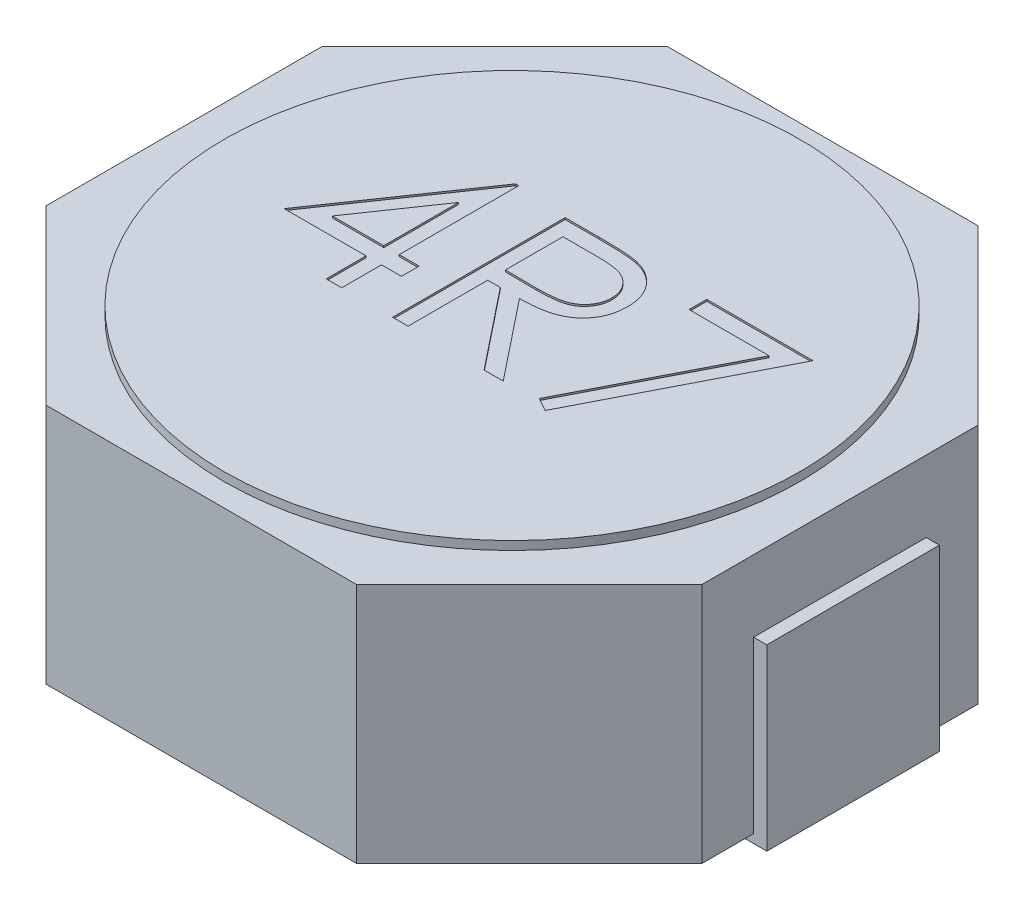
SolidWorks part; units mm, degrees
ref_plane "Front Plane" through (0, 0, 0) normal (0, 0, 1) x (1, 0, 0)
ref_plane "Top Plane" through (0, 0, 0) normal (0, 1, 0) x (1, 0, 0)
ref_plane "Right Plane" through (0, 0, 0) normal (1, 0, 0) x (0, 0, -1)
sketch "Sketch1" plane through (0, 0, 0) normal (0, 1, 0) x (1, 0, 0)
  line L0 (-0.9, 1.8) -> (-1.9, 0.8)
  line L1 (-0.9, 1.8) -> (0.9, 1.8)
  line L2 (-1.9, 0.8) -> (-1.9, -0.8)
  line L3 (-0.9, -1.8) -> (0.9, -1.8)
  line L4 (1.9, 0.8) -> (1.9, -0.8)
  line L5 (-1.9, 1.8) -> (1.9, -1.8) construction
  line L6 (-1.9, -1.8) -> (1.9, 1.8) construction
  line L7 (0.9, -1.8) -> (1.9, -0.8)
  line L8 (0.9, 1.8) -> (1.9, 0.8)
  line L9 (-1.9, -0.8) -> (-0.9, -1.8)
  point P0 (0, 0)
  dimension "D1" = 3.8
  dimension "D2" = 3.6
extrude "Boss-Extrude1" add sketch "Sketch1" along normal blind 1.4
sketch "Sketch2" plane through (0, 1.4, 0) normal (0, 1, 0) x (1, 0, 0)
  circle A0 centre (0, 0) radius 1.6679
extrude "Boss-Extrude2" add sketch "Sketch2" along normal blind 0.05
sketch "Sketch3" plane through (0, 0, 0) normal (0, 0, 1) x (1, 0, 0)
  line L0 (-1.9764, 0.9857) -> (-1.9764, -0.0499)
  line L1 (-1.9764, -0.0499) -> (-1.2507, -0.0499)
extrude "Extrude-Thin1" add sketch "Sketch3" along normal mid plane 1 thin thin type one direction reverse wall 0.1
mirror "Mirror1" about plane through (0, 0, 0) normal (1, 0, 0) of "Extrude-Thin1"
sketch "Sketch4" plane through (0, 1.45, 0) normal (0, 1, 0) x (1, 0, 0)
  text T0 "4R7" font "Century Gothic" height 1
extrude "Cut-Extrude1" cut sketch "Sketch4" against normal blind 0.01
